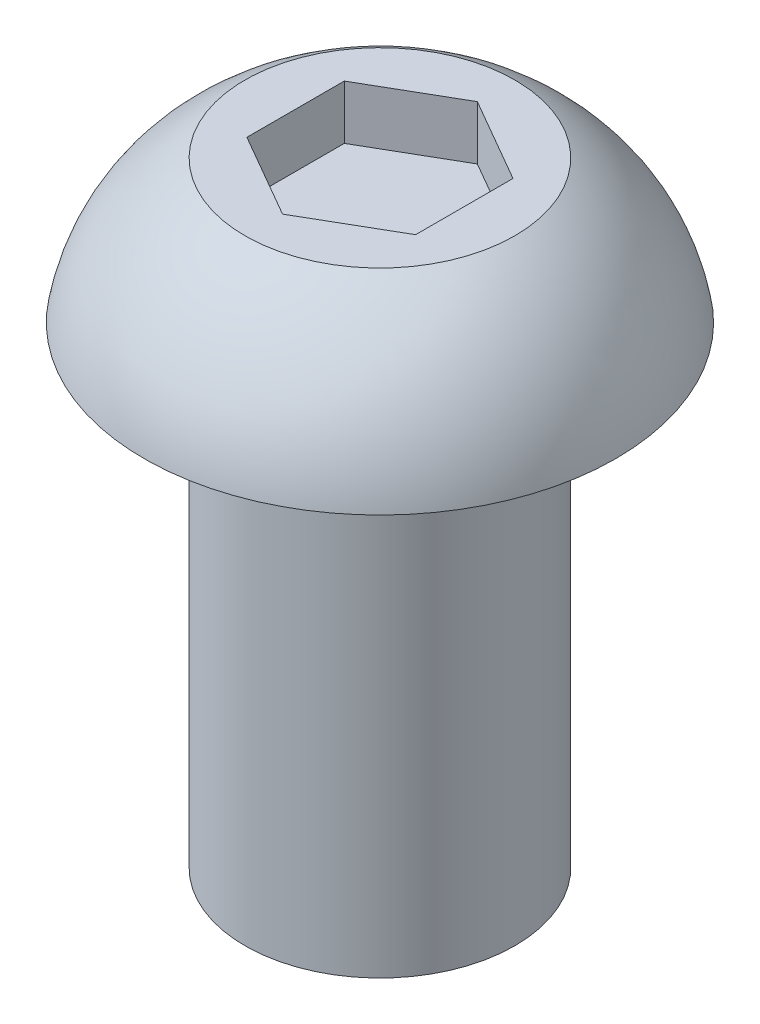
SolidWorks part; units mm, degrees
material "AISI Type 316L stainless steel"
ref_plane "Front Plane" through (0, 0, 0) normal (0, 0, 1) x (1, 0, 0)
ref_plane "Top Plane" through (0, 0, 0) normal (0, 1, 0) x (1, 0, 0)
ref_plane "Right Plane" through (0, 0, 0) normal (1, 0, 0) x (0, 0, -1)
sketch "Sketch1" plane through (0, 0, 0) normal (0, 0, 1) x (1, 0, 0)
  line L0 (-3.175, 0) -> (-5.5499, 0)
  line L1 (-3.175, 0) -> (-3.175, -11.1125)
  line L2 (0, -11.1125) -> (0, 3.3528)
  line L3 (0, 3.3528) -> (-3.175, 3.3528)
  line L4 (-3.175, -11.1125) -> (0, -11.1125)
  arc A0 (-5.5499, 0) -> (-3.175, 3.3528) centre (-0.9016, -0.775) cw
  dimension "D1" = 11.1125
  dimension "D2" = 3.3528
  dimension "D3" = 5.5499
  dimension "D4" = 3.175
  dimension "D5" = 3.175
revolve "Revolve1" add sketch "Sketch1" angle 360 about L2
sketch "Sketch2" plane through (0, 3.3528, 0) normal (0, 1, 0) x (1, 0, 0)
  line L0 (0, 0) -> (0, 2.2914) construction
  line L1 (-1.9844, 1.1457) -> (-1.9844, -1.1457)
  line L2 (-1.9844, -1.1457) -> (0, -2.2914)
  line L3 (0, -2.2914) -> (1.9844, -1.1457)
  line L4 (1.9844, -1.1457) -> (1.9844, 1.1457)
  line L5 (1.9844, 1.1457) -> (0, 2.2914)
  line L6 (0, 2.2914) -> (-1.9844, 1.1457)
  circle A0 centre (0, 0) radius 1.9844 construction
  dimension "D1" = 3.9688
extrude "Cut-Extrude1" cut sketch "Sketch2" against normal blind 1.27
